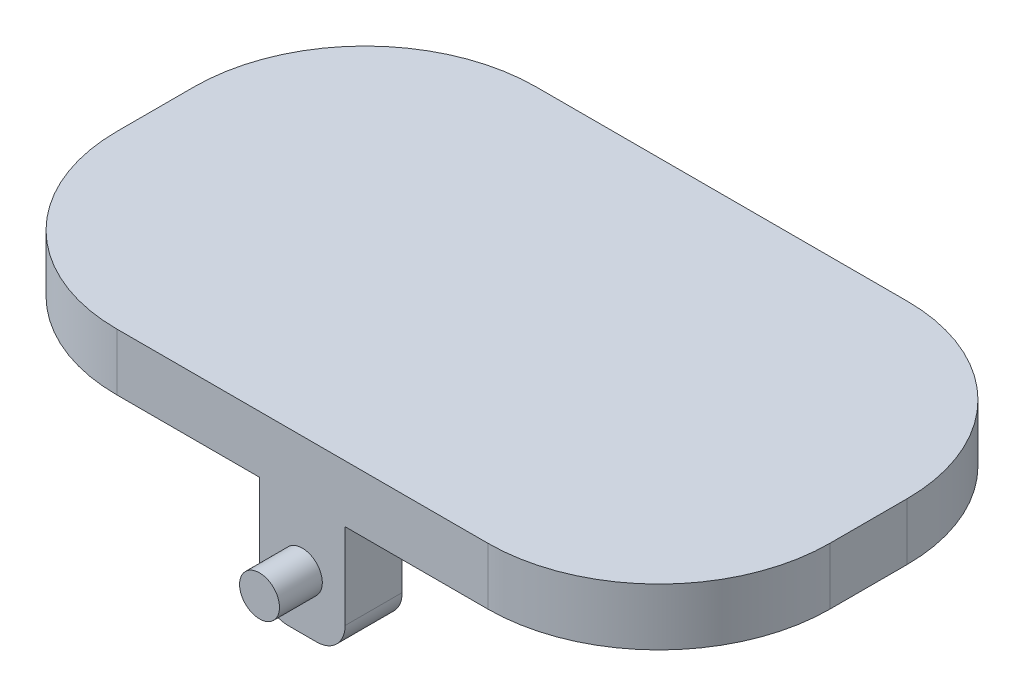
SolidWorks part; units mm, degrees
ref_plane "Front Plane" through (0, 0, 0) normal (0, 0, 1) x (1, 0, 0)
ref_plane "Top Plane" through (0, 0, 0) normal (0, 1, 0) x (1, 0, 0)
ref_plane "Right Plane" through (0, 0, 0) normal (1, 0, 0) x (0, 0, -1)
sketch "Sketch1" plane through (0, 0, 0) normal (0, 1, 0) x (1, 0, 0)
  line L1 (-12.5, 7.35) -> (12.5, 7.35)
  line L2 (-12.5, 7.35) -> (-12.5, -7.35)
  line L3 (-12.5, -7.35) -> (12.5, -7.35)
  line L4 (12.5, 7.35) -> (12.5, -7.35)
  line L5 (0, -7.35) -> (0, 7.35) construction
  line L6 (-12.5, 0) -> (12.5, 0) construction
  point P0 (0, 0)
  dimension "D1" = 25
  dimension "D2" = 14.7
extrude "Boss-Extrude1" add sketch "Sketch1" along normal blind 2
fillet "Fillet1" radius 6 4 edges at (-12.5, 1, 7.35) (-12.5, 1, -7.35) (12.5, 1, -7.35) (12.5, 1, 7.35)
sketch "Sketch3" plane through (0, 0, -7.35) normal (0, 0, -1) x (-1, 0, 0)
  line L0 (-1.5, 0) -> (-1.5, -3)
  line L1 (-6.5, 0) -> (6.5, 0) construction
  line L2 (-0.5, -4) -> (0.5, -4)
  line L3 (1.5, -3) -> (1.5, 0)
  line L4 (1.5, 0) -> (-1.5, 0)
  arc A1 (-1.5, -3) -> (-0.5, -4) centre (-0.5, -3) ccw
  arc A2 (0.5, -4) -> (1.5, -3) centre (0.5, -3) ccw
  point P4 (0, 0)
  point P7 (0, 0)
  dimension "D4" = 1
  dimension "D1" = 3
  dimension "D2" = 4
extrude "Boss-Extrude6" add sketch "Sketch3" against normal blind 2
sketch "Sketch5" plane through (0, 0, -7.35) normal (0, 0, -1) x (-1, 0, 0)
  circle A0 centre (0, -2.1) radius 0.7
  dimension "D2" = 1.4
  dimension "D1" = 2.1
extrude "Boss-Extrude7" add sketch "Sketch5" along normal blind 1.5
mirror "Mirror3" about plane through (0, 0, 0) normal (0, 0, 1) of "Boss-Extrude7", "Boss-Extrude6"
